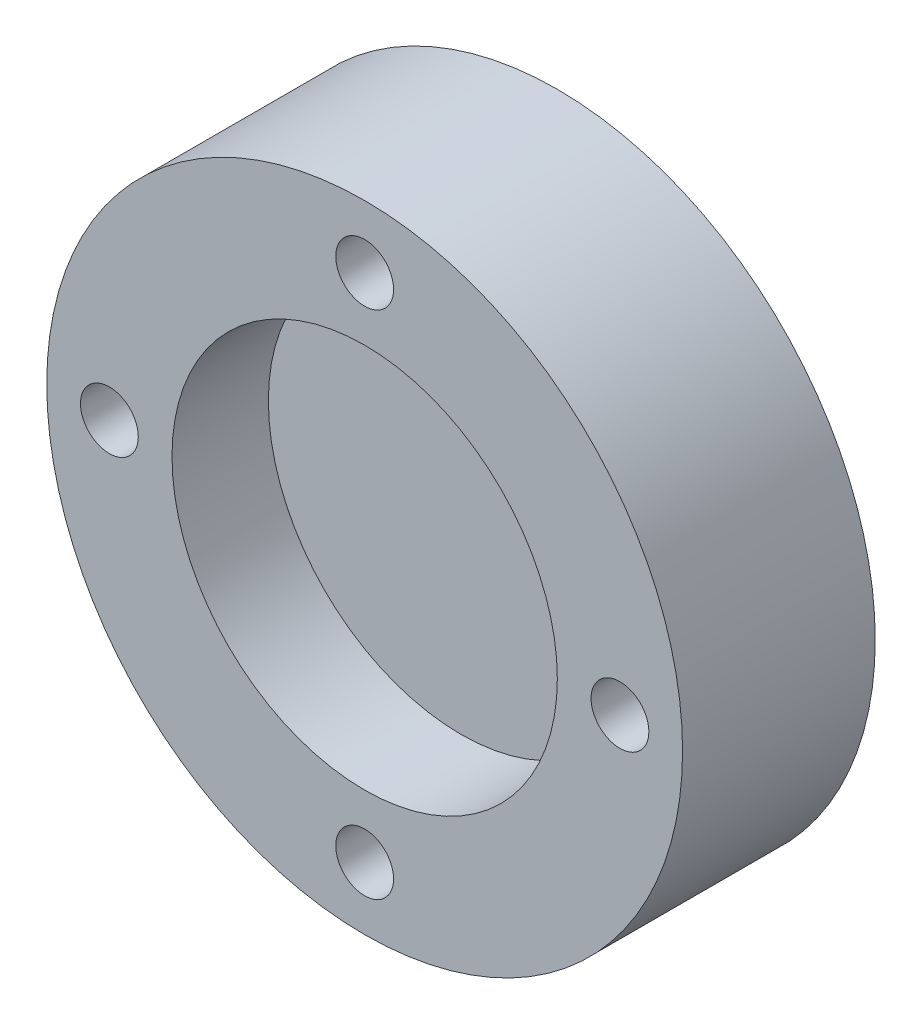
SolidWorks part; units mm, degrees
ref_plane "Ön Düzlem" through (0, 0, 0) normal (0, 0, 1) x (1, 0, 0)
ref_plane "Üst Düzlem" through (0, 0, 0) normal (0, 1, 0) x (1, 0, 0)
ref_plane "Sağ Düzlem" through (0, 0, 0) normal (1, 0, 0) x (0, 0, -1)
sketch "Çizim1" plane through (0, 0, 0) normal (0, 0, 1) x (1, 0, 0)
  line L0 (0, 20.7858) -> (0, -26.0819) construction
  line L1 (-23.5623, 0) -> (42.1685, 0) construction
  circle A0 centre (0, 0) radius 16.5
  circle A1 centre (0, 0) radius 10
  circle A2 centre (0, 13.25) radius 1.5
  circle A3 centre (13.25, 0) radius 1.5
  circle A4 centre (0, -13.25) radius 1.5
  circle A5 centre (-13.25, 0) radius 1.5
  dimension "D1" = 33
  dimension "D2" = 20
  dimension "D3" = 13.25
  dimension "D4" = 3
  dimension "D5" = 13.25
  dimension "D6" = 13.25
  dimension "D7" = 13.25
extrude "Yükseklik-Ekstrüzyon1" add sketch "Çizim1" against normal blind 10
ref_plane "Düzlem1" through (0, 0, -10) normal (0, 0, -1) x (-1, 0, 0)
sketch "Çizim2" plane through (0, 0, -10) normal (0, 0, -1) x (-1, 0, 0)
  circle A0 centre (0, 0) radius 9.998
  dimension "D1" = 19.996
extrude "Yükseklik-Ekstrüzyon2" add sketch "Çizim2" against normal blind 5 separate body
sketch "Çizim4" plane through (0, 0, -10) normal (0, 0, -1) x (-1, 0, 0)
  circle A0 centre (0, 0) radius 9.998
extrude "Yükseklik-Ekstrüzyon3" add sketch "Çizim4" along normal blind 2
